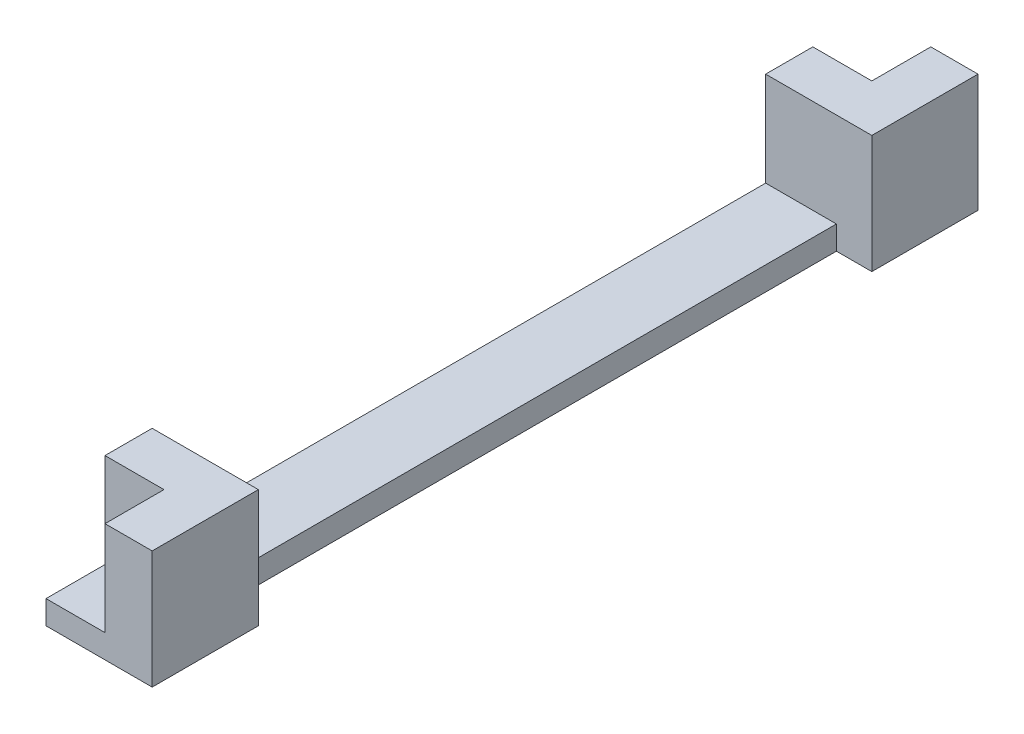
SolidWorks part; units mm, degrees
ref_plane "Plano frontal" through (0, 0, 0) normal (0, 0, 1) x (1, 0, 0)
ref_plane "Plano superior" through (0, 0, 0) normal (0, 1, 0) x (1, 0, 0)
ref_plane "Plano direito" through (0, 0, 0) normal (1, 0, 0) x (0, 0, -1)
sketch "Esboço1" plane through (0, 0, 0) normal (0, 1, 0) x (1, 0, 0)
  line L1 (-4.5, -35) -> (4.5, -35)
  line L2 (-4.5, -35) -> (-4.5, 35)
  line L3 (-4.5, 35) -> (4.5, 35)
  line L4 (4.5, -35) -> (4.5, 35)
  line L5 (-4.5, -35) -> (4.5, 35) construction
  line L6 (-4.5, 35) -> (4.5, -35) construction
  line L7 (-4.5, 35) -> (0.5, 35)
  line L8 (-4.5, 35) -> (-4.5, 30)
  line L9 (-4.5, 30) -> (0.5, 30)
  line L10 (0.5, 35) -> (0.5, 30)
  line L11 (-4.5, 35) -> (4.5, 35)
  line L12 (-4.5, 35) -> (-4.5, 26)
  line L13 (-4.5, 26) -> (4.5, 26)
  line L14 (4.5, 35) -> (4.5, 26)
  line L15 (-4.5, -35) -> (0.5, -35)
  line L16 (-4.5, -35) -> (-4.5, -30)
  line L17 (-4.5, -30) -> (0.5, -30)
  line L18 (0.5, -35) -> (0.5, -30)
  line L19 (-4.5, -35) -> (4.5, -35)
  line L20 (-4.5, -35) -> (-4.5, -26)
  line L21 (-4.5, -26) -> (4.5, -26)
  line L22 (4.5, -35) -> (4.5, -26)
  point P0 (0, 0)
  dimension "D1" = 70
  dimension "D2" = 4
  dimension "D3" = 5
  dimension "D4" = 5
  dimension "D5" = 4
  dimension "D6" = 4
  dimension "D7" = 5
  dimension "D8" = 5
  dimension "D9" = 4
extrude "Ressalto-extrusão1" add sketch "Esboço1" along normal blind 10 contours L21 L2 L17 L18 L1 L4 | L2 L13 L4 L3 L10 L9
sketch "Esboço2" plane through (0, 0, 0) normal (0, 1, 0) x (1, 0, 0)
  line L0 (-4.5, -30) -> (-4.5, -26) construction
  line L1 (4.5, 35) -> (-4.5, 35)
  line L2 (4.5, 35) -> (4.5, -35)
  line L3 (4.5, -35) -> (-4.5, -35)
  line L4 (-4.5, 35) -> (-4.5, -35)
  line L5 (0.5, -35) -> (4.5, -35) construction
extrude "Ressalto-extrusão2" add sketch "Esboço2" along normal blind 2
sketch "Esboço3" plane through (0, 2, 0) normal (0, 1, 0) x (1, 0, 0)
  line L0 (-4.5, -26) -> (4.5, -26) construction
  line L1 (4.5, 26) -> (1.5, 26)
  line L2 (4.5, 26) -> (4.5, -26)
  line L3 (4.5, -26) -> (1.5, -26)
  line L4 (1.5, 26) -> (1.5, -26)
  dimension "D1" = 3
extrude "Corte-extrusão1" cut sketch "Esboço3" against normal through all
